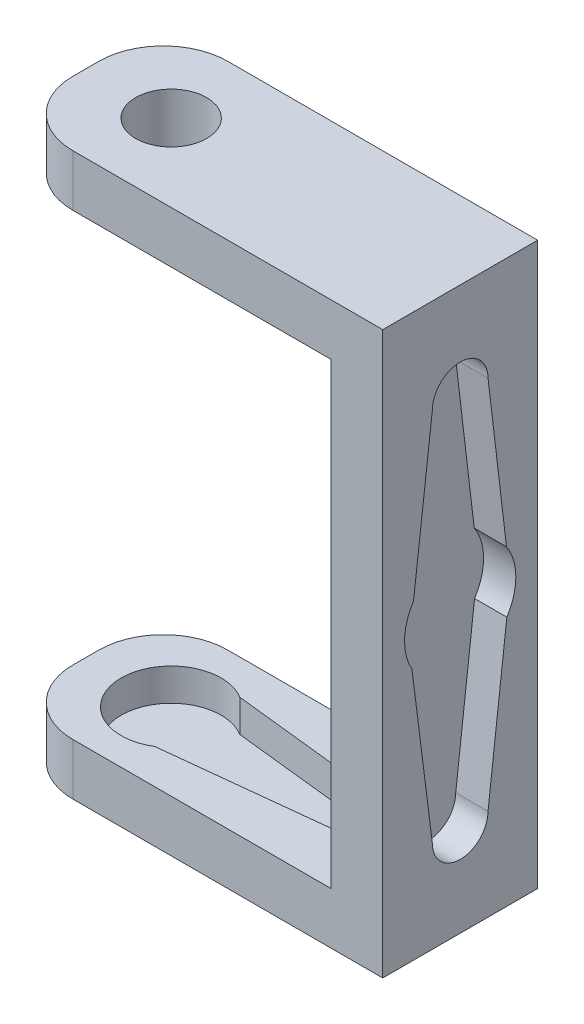
SolidWorks part; units mm, degrees
ref_plane "Front Plane" through (0, 0, 0) normal (0, 0, 1) x (1, 0, 0)
ref_plane "Top Plane" through (0, 0, 0) normal (0, 1, 0) x (1, 0, 0)
ref_plane "Right Plane" through (0, 0, 0) normal (1, 0, 0) x (0, 0, -1)
sketch "Sketch1" plane through (0, 0, 0) normal (0, 1, 0) x (1, 0, 0)
  line L0 (0, 0) -> (15.85, 0) construction
  line L4 (14.2541, 1.9624) -> (2.0291, 3.2998)
  line L5 (14.2541, -1.9624) -> (2.0291, -3.2998)
  arc A12 (2.0291, 3.2998) -> (2.0291, -3.2998) centre (0, 0) ccw
  arc A13 (14.2541, -1.9624) -> (14.2541, 1.9624) centre (14.2541, 0) ccw
  point P1 (0, 0)
  point P3 (14.2541, 1.9624)
  point P6 (2.0291, -3.2998)
sketch3d "3DSketch2" plane through (0, 0, 0) normal (0, 0, 1) x (1, 0, 0)
  dimension "D1" = 1.5
sketch "Sketch3" plane through (0, 0, 0) normal (0, 1, 0) x (1, 0, 0)
  line L1 (-6.6092, 6) -> (18.3908, 6)
  line L2 (-6.6092, 6) -> (-6.6092, -6)
  line L3 (-6.6092, -6) -> (18.3908, -6)
  line L4 (18.3908, 6) -> (18.3908, -6)
  line L5 (0, 0) -> (15.85, 0) construction
  dimension "D1" = 25
  dimension "D2" = 12
  dimension "D3" = 6
  dimension "D4" = 18.3908
extrude "Boss-Extrude1" add sketch "Sketch3" against normal blind 4
extrude "single horn" cut sketch "Sketch1" against normal blind 2.5
sketch "Sketch4" plane through (0, -4, 0) normal (0, -1, 0) x (1, 0, 0)
  line L1 (18.3908, 6) -> (22.3908, 6)
  line L2 (18.3908, 6) -> (18.3908, -6)
  line L3 (18.3908, -6) -> (22.3908, -6)
  line L4 (22.3908, 6) -> (22.3908, -6)
extrude "Boss-Extrude2" add sketch "Sketch4" against normal blind 43.5
sketch "Sketch5" plane through (0, 39.5, 0) normal (0, 1, 0) x (1, 0, 0)
  line L1 (18.3908, 6) -> (-6.6092, 6)
  line L2 (18.3908, 6) -> (18.3908, -6)
  line L3 (18.3908, -6) -> (-6.6092, -6)
  line L4 (-6.6092, 6) -> (-6.6092, -6)
extrude "Boss-Extrude4" add sketch "Sketch5" against normal blind 4 contours L3 L4 L1 L2
sketch "Sketch6" plane through (0, 39.5, 0) normal (0, 1, 0) x (1, 0, 0)
  circle A0 centre (0, 0) radius 2.75
  dimension "D1" = 5.5
extrude "Cut-Extrude3" cut sketch "Sketch6" against normal blind 4
fillet "Fillet1" radius 5 4 edges at (-6.6092, -2, -6) (-6.6092, 37.5, 6) (-6.6092, 37.5, -6) (-6.6092, -2, 6)
sketch "Sketch11" plane through (22.3908, 0, 0) normal (1, 0, 0) x (0, 0, -1)
  line L0 (0, 17.75) -> (0, 33.6) construction
  line L1 (-2.1545, 32.1716) -> (-3.6153, 20.0991)
  line L2 (3.5878, 20.1409) -> (2.1564, 32.1716)
  line L3 (6, -4) -> (-6, -4) construction
  line L4 (0.001, 17.4596) -> (0.001, 1.6096) construction
  line L5 (2.1564, 3.1096) -> (3.6153, 15.4009)
  line L6 (-3.7385, 15.6023) -> (-2.1545, 3.1096)
  arc A0 (-3.6153, 20.0991) -> (-3.7385, 15.6023) centre (0, 17.75) ccw
  arc A9 (2.1564, 32.1716) -> (-2.1545, 32.1716) centre (0.001, 32.1716) ccw
  arc A16 (-2.1545, 3.1096) -> (2.1564, 3.1096) centre (0.001, 3.1096) ccw
  arc A17 (3.6153, 15.4009) -> (3.5878, 20.1409) centre (0, 17.75) ccw
  point P2 (0, 0)
  point P3 (0, 0)
  point P8 (0, 0)
  point P9 (0, 0)
  point P10 (0, 0)
  point P11 (0, 0)
  point P12 (0, 0)
  point P13 (0, 0)
  point P15 (0, 0)
  point P18 (0, 0)
  point P19 (0, 0)
  point P20 (0, 0)
  dimension "D1" = 21.75
extrude "double horn" cut sketch "Sketch11" against normal blind 2.5
